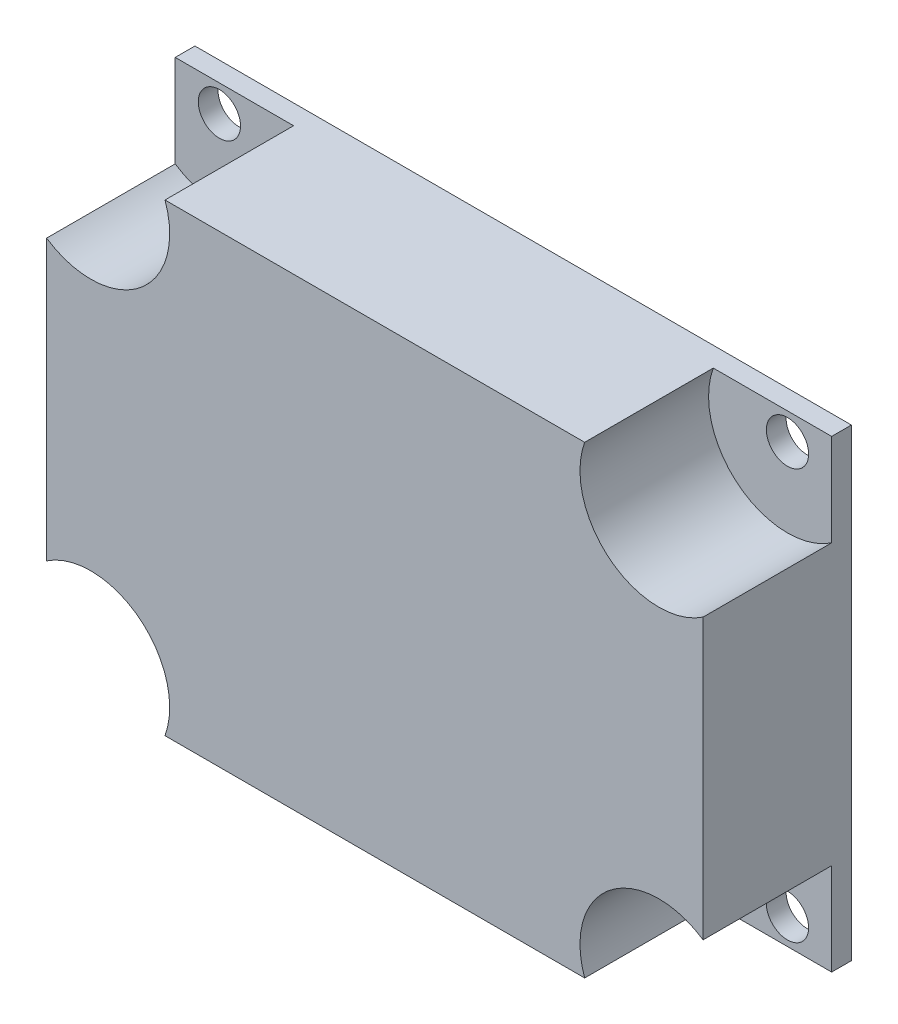
SolidWorks part; units mm, degrees
ref_plane "Front Plane" through (0, 0, 0) normal (0, 0, 1) x (1, 0, 0)
ref_plane "Top Plane" through (0, 0, 0) normal (0, 1, 0) x (1, 0, 0)
ref_plane "Right Plane" through (0, 0, 0) normal (1, 0, 0) x (0, 0, -1)
sketch "Sketch1" plane through (0, 0, 0) normal (0, 0, 1) x (1, 0, 0)
  line L1 (-26.416, 18.669) -> (26.416, 18.669)
  line L2 (-26.416, 18.669) -> (-26.416, -18.669)
  line L3 (-26.416, -18.669) -> (26.416, -18.669)
  line L4 (26.416, 18.669) -> (26.416, -18.669)
  line L5 (-26.416, 18.669) -> (26.416, -18.669) construction
  line L6 (-26.416, -18.669) -> (26.416, 18.669) construction
  point P0 (0, 0)
  dimension "D1" = 52.832
  dimension "D2" = 37.338
extrude "Boss-Extrude1" add sketch "Sketch1" along normal blind 11.938
hole_wizard "M3 Clearance Hole1" positions "Sketch2" profile "Sketch3" hole size "M3" standard "ANSI Metric" end condition up to next
sketch "Sketch2" plane through (0, 0, 11.938) normal (0, 0, 1) x (1, 0, 0)
  line L1 (22.86, -16.51) -> (-22.86, -16.51)
  line L2 (22.86, -16.51) -> (22.86, 16.51)
  line L3 (22.86, 16.51) -> (-22.86, 16.51)
  line L4 (-22.86, -16.51) -> (-22.86, 16.51)
  line L5 (22.86, -16.51) -> (-22.86, 16.51) construction
  line L6 (22.86, 16.51) -> (-22.86, -16.51) construction
  line L7 (26.416, 18.669) -> (-26.416, 18.669) construction
  line L8 (26.416, -18.669) -> (26.416, 18.669) construction
  point P0 (-22.86, 16.51)
  point P89 (22.86, -16.51)
  point P90 (22.86, 16.51)
  point P91 (-22.86, -16.51)
  point P102 (0, 0)
  dimension "D1" = 33.02
  dimension "D2" = 45.72
  dimension "D3" = 2.159
  dimension "D4" = 3.556
sketch "Sketch3" plane through (-22.86, 16.51, 11.938) normal (1, 0, 0) x (0, -1, 0)
  line L0 (0, 0) -> (0, 11.938)
  line L1 (0, 11.938) -> (1.7, 11.938)
  line L2 (1.7, 11.938) -> (1.7, 0)
  line L5 (1.7, 0) -> (0, 0)
  line L11 (0, -6.35) -> (0, 107.95) construction
  dimension "Thru Hole Dia." = 3.4
  dimension "Thru Hole Depth" = 11.938
sketch "Sketch4" plane through (0, 0, 11.938) normal (0, 0, 1) x (1, 0, 0)
  circle A0 centre (-22.86, 16.51) radius 6.35
  circle A1 centre (-22.86, -16.51) radius 6.35
  circle A2 centre (22.86, 16.51) radius 6.35
  circle A3 centre (22.86, -16.51) radius 6.35
  dimension "D1" = 12.7
extrude "Cut-Extrude1" cut sketch "Sketch4" against normal blind 10.3505
